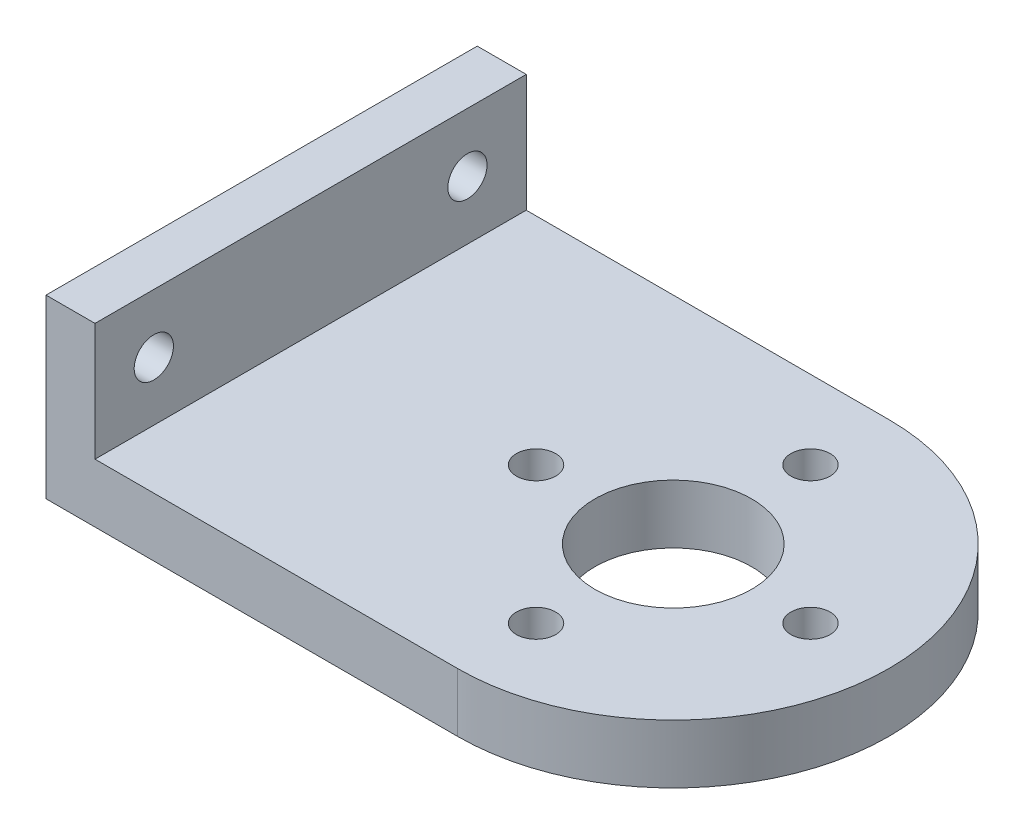
SolidWorks part; units mm, degrees
ref_plane "Front Plane" through (0, 0, 0) normal (0, 0, 1) x (1, 0, 0)
ref_plane "Top Plane" through (0, 0, 0) normal (0, 1, 0) x (1, 0, 0)
ref_plane "Right Plane" through (0, 0, 0) normal (1, 0, 0) x (0, 0, -1)
sketch "Sketch1" plane through (0, 0, 0) normal (0, 1, 0) x (1, 0, 0)
  line L0 (-28.2208, 0) -> (26.2745, 0) construction
  line L2 (-14, -11) -> (-14, 11)
  line L5 (-14, 11) -> (7, 11)
  line L6 (7, -11) -> (-14, -11)
  circle A0 centre (7, -7) radius 1
  circle A1 centre (0, 0) radius 1
  circle A2 centre (7, 0) radius 4
  arc A3 (7, -11) -> (7, 11) centre (7, 0) ccw
  circle A4 centre (14, 0) radius 1
  circle A5 centre (14, 0) radius 1
  circle A6 centre (14, 0) radius 1
  circle A7 centre (14, 0) radius 1
  circle A8 centre (7, 7) radius 1
  point P0 (0, 0)
  point P6 (-14, 0)
  point P26 (14, 0)
  point P29 (7, 0)
  dimension "D3" = 8
  dimension "D5" = 22
  dimension "D6" = 4
  dimension "D12" = 2
  dimension "D2" = 22
  dimension "D4" = 21
  dimension "D11" = 7
  dimension "D13" = 4
extrude "Boss-Extrude1" add sketch "Sketch1" along normal blind 3 contours L2 L0 A1 A2 A4 A3 L5 A8 | L0 L2 L6 A3 A7 A2 A1 A0
sketch "Sketch2" plane through (0, 3, 0) normal (0, 1, 0) x (1, 0, 0)
  line L0 (-14, 11) -> (-11.5, 11)
  line L1 (-14, 11) -> (7, 11) construction
  line L2 (-11.5, 11) -> (-11.5, -11)
  line L3 (7, -11) -> (-14, -11) construction
  line L4 (-11.5, -11) -> (-14, -11)
  line L5 (-14, -11) -> (-14, 11)
  dimension "D1" = 2.5
extrude "Boss-Extrude2" add sketch "Sketch2" along normal blind 6
sketch "Sketch3" plane through (-11.5, 0, 0) normal (1, 0, 0) x (0, 0, -1)
  line L0 (11, 9) -> (11, 3) construction
  line L1 (-11, 9) -> (-11, 3) construction
  line L2 (-11, 9) -> (11, 9) construction
  circle A0 centre (8, 6) radius 1
  circle A1 centre (-8, 6) radius 1
  dimension "D1" = 2
  dimension "D2" = 2
  dimension "D3" = 3
  dimension "D4" = 3
  dimension "D5" = 3
  dimension "D6" = 3
extrude "Cut-Extrude1" cut sketch "Sketch3" against normal blind 6
